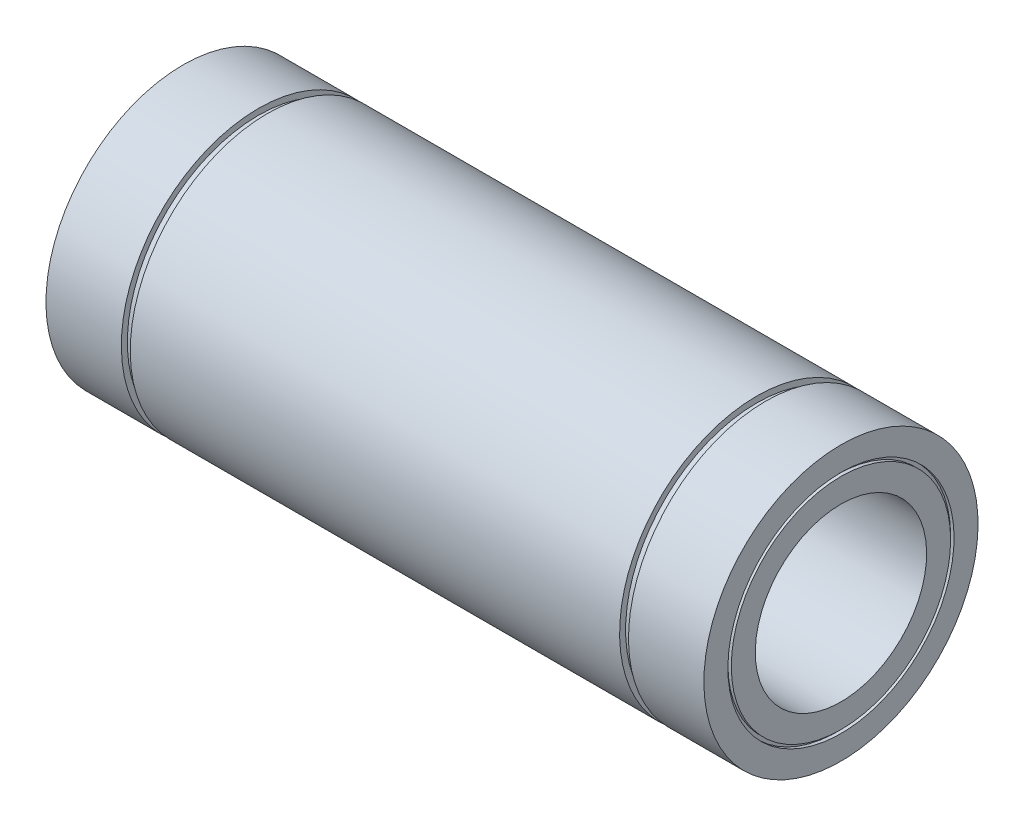
SolidWorks part; units mm, degrees
material "Ст3сп ГОСТ 535-2005"
ref_plane "Plano frontal" through (0, 0, 0) normal (0, 0, 1) x (1, 0, 0)
ref_plane "Plano superior" through (0, 0, 0) normal (0, 1, 0) x (1, 0, 0)
ref_plane "Plano direito" through (0, 0, 0) normal (1, 0, 0) x (0, 0, -1)
sketch "Esboço1" plane through (0, 0, 0) normal (0, 0, 1) x (1, 0, 0)
  line L0 (-96, 40) -> (-74, 40)
  line L1 (-74, 40) -> (-74, 38.25)
  line L2 (-74, 38.25) -> (-71.4, 38.25)
  line L3 (-71.4, 38.25) -> (-71.4, 40)
  line L4 (-71.4, 40) -> (71.4, 40)
  line L5 (71.4, 40) -> (71.4, 38.25)
  line L6 (71.4, 38.25) -> (74, 38.25)
  line L7 (74, 38.25) -> (74, 40)
  line L8 (74, 40) -> (96, 40)
  line L9 (96, 40) -> (96, 33)
  line L10 (96, 25) -> (-96, 25)
  line L11 (-96, 25) -> (-96, 32)
  line L12 (0, 25) -> (0, 0) construction
  line L13 (0, 0) -> (-86.5, 0) construction
  line L14 (-96, 33) -> (-96, 40)
  line L15 (-96, 33) -> (-95, 33)
  line L16 (96, 32) -> (96, 25)
  line L17 (-95, 33) -> (-95, 32)
  line L18 (-95, 32) -> (-96, 32)
  line L19 (96, 33) -> (95, 33)
  line L21 (96, 32) -> (95, 32)
  line L22 (95, 33) -> (95, 32)
  dimension "D1" = 192
  dimension "D2" = 148
  dimension "D3" = 2.6
  dimension "D4" = 50
  dimension "D5" = 80
  dimension "D6" = 76.5
  dimension "D7" = 1
  dimension "D8" = 1
  dimension "D9" = 1
  dimension "D10" = 1
revolve "Revolução1" add sketch "Esboço1" angle 360 about L13
